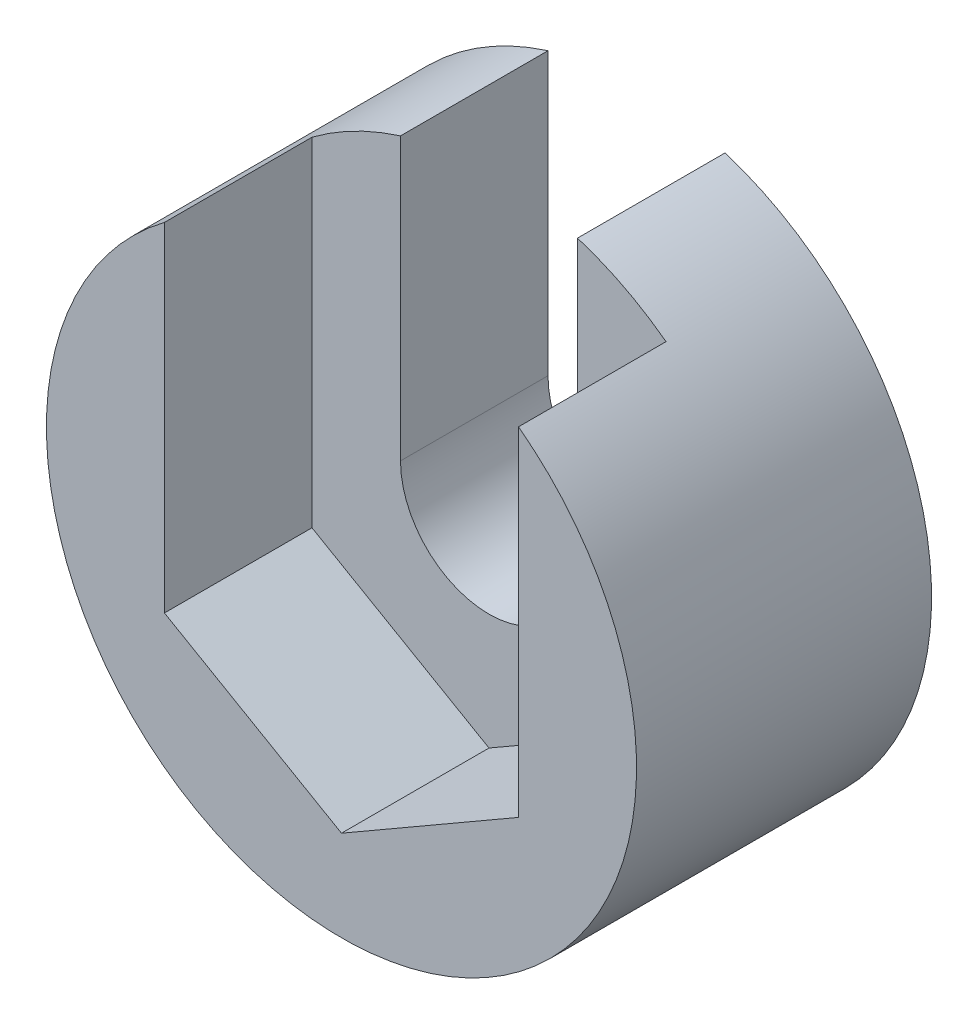
SolidWorks part; units mm, degrees
ref_plane "Płaszczyzna przednia" through (0, 0, 0) normal (0, 0, 1) x (1, 0, 0)
ref_plane "Płaszczyzna górna" through (0, 0, 0) normal (0, 1, 0) x (1, 0, 0)
ref_plane "Płaszczyzna prawa" through (0, 0, 0) normal (1, 0, 0) x (0, 0, -1)
sketch "Szkic1" plane through (0, 0, 0) normal (0, 0, 1) x (1, 0, 0)
  circle A0 centre (0, 0) radius 5
extrude "Dodanie-wyciągnięcie1" add sketch "Szkic1" along normal blind 5
sketch "Szkic10" plane through (0, 0, 5) normal (0, 0, 1) x (1, 0, 0)
  line L1 (0, 3.4641) -> (-3, 1.7321)
  line L2 (-3, 1.7321) -> (-3, -1.7321)
  line L3 (-3, -1.7321) -> (0, -3.4641)
  line L4 (0, -3.4641) -> (3, -1.7321)
  line L5 (3, -1.7321) -> (3, 1.7321)
  line L6 (3, 1.7321) -> (0, 3.4641)
  circle A0 centre (0, 0) radius 3 construction
  dimension "D1" = 6
extrude "Wytnij-wyciągnięcie3" cut sketch "Szkic10" against normal blind 2.5
hole_wizard "Otwory ustalające Ø3.0mmClearance 1" positions "Szkic11" profile "Szkic12" hole size "Ø3.0" standard "Ansi Metric"
sketch "Szkic11" plane through (0, 0, 2.5) normal (0, 0, 1) x (1, 0, 0)
  point P0 (0, 0)
sketch "Szkic12" plane through (0, 0, 2.5) normal (1, 0, 0) x (0, -1, 0)
  line L0 (0, 0) -> (0, 8.1513)
  line L1 (0, 8.1513) -> (1.5, 7.25)
  line L2 (1.5, 7.25) -> (1.5, 0)
  line L5 (1.5, 0) -> (0, 0)
  line L10 (0, 8.1513) -> (-1.5, 7.25) construction
  line L11 (0, -6.35) -> (0, 107.95) construction
  dimension "Średnica otworu" = 3
  dimension "Głębokość otworu" = 7.25
  dimension "Kąt wiertła" = 118
sketch "Szkic19" plane through (0, 0, 5) normal (0, 0, 1) x (1, 0, 0)
  line L0 (-3, 1.7321) -> (3, 1.7321)
  line L1 (-3, 1.7321) -> (-3, 5.3949)
  line L2 (3, 1.7321) -> (3, 5.3949)
  line L3 (-3, 5.3949) -> (3, 5.3949)
extrude "Wytnij-wyciągnięcie8" cut sketch "Szkic19" against normal blind 2.5
sketch "Szkic20" plane through (0, 0, 2.5) normal (0, 0, 1) x (1, 0, 0)
  line L4 (1.5, 0) -> (-1.5, 0)
  line L5 (1.5, 0) -> (1.5, 6.977)
  line L6 (-1.5, 0) -> (-1.5, 6.977)
  line L7 (1.5, 6.977) -> (-1.5, 6.977)
  circle A1 centre (0, 0) radius 1.5 construction
extrude "Wytnij-wyciągnięcie9" cut sketch "Szkic20" against normal blind 2.5
